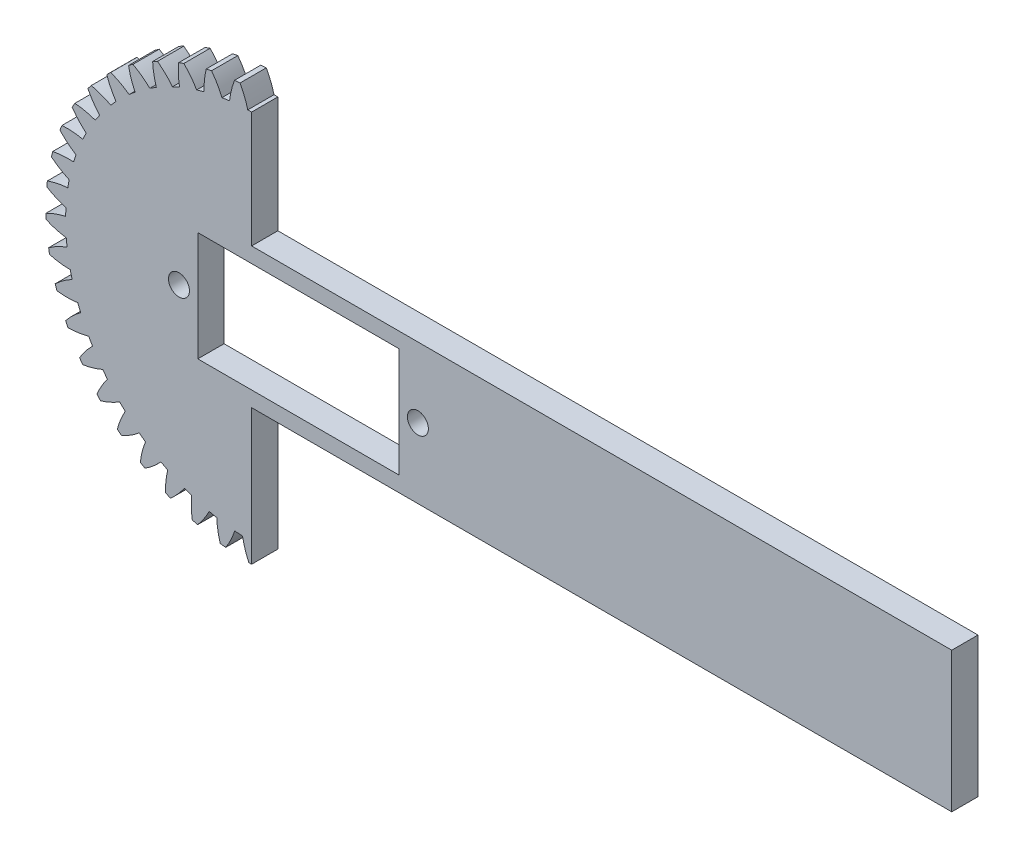
SolidWorks part; units mm, degrees
ref_plane "Front Plane" through (0, 0, 0) normal (0, 0, 1) x (1, 0, 0)
ref_plane "Top Plane" through (0, 0, 0) normal (0, 1, 0) x (1, 0, 0)
ref_plane "Right Plane" through (0, 0, 0) normal (1, 0, 0) x (0, 0, -1)
sketch "Model" plane through (0, 0, 0) normal (0, 0, 1) x (1, 0, 0)
  circle A0 centre (55.7791, 90.651) radius 15.95 construction
  arc A1 (32.4426, 93.4186) -> (32.3772, 92.7957) centre (55.7791, 90.651) ccw
  arc A2 (34.7806, 93.9041) -> (32.4426, 93.4186) centre (35.4255, 84.9273) ccw
  arc A3 (34.9343, 94.7759) -> (34.7806, 93.9041) centre (55.7791, 90.651) ccw
  arc A4 (32.9034, 96.0318) -> (34.9343, 94.7759) centre (38.6106, 102.9908) ccw
  arc A5 (33.0549, 96.6395) -> (32.9034, 96.0318) centre (55.7791, 90.651) ccw
  arc A6 (35.4377, 96.7949) -> (33.0549, 96.6395) centre (34.827, 87.8157) ccw
  arc A7 (35.7112, 97.6368) -> (35.4377, 96.7949) centre (55.7791, 90.651) ccw
  arc A8 (33.8749, 99.1631) -> (35.7112, 97.6368) centre (40.495, 105.2601) ccw
  arc A9 (34.1095, 99.7438) -> (33.8749, 99.1631) centre (55.7791, 90.651) ccw
  arc A10 (36.4907, 99.5661) -> (34.1095, 99.7438) centre (34.6363, 90.7592) ccw
  arc A11 (36.8788, 100.3617) -> (36.4907, 99.5661) centre (55.7791, 90.651) ccw
  arc A12 (35.2727, 102.1287) -> (36.8788, 100.3617) centre (42.677, 107.2451) ccw
  arc A13 (35.5859, 102.6711) -> (35.2727, 102.1287) centre (55.7791, 90.651) ccw
  arc A14 (37.9192, 102.1637) -> (35.5859, 102.6711) centre (34.8571, 93.7007) ccw
  arc A15 (38.4142, 102.8976) -> (37.9192, 102.1637) centre (55.7791, 90.651) ccw
  arc A16 (37.0697, 104.871) -> (38.4142, 102.8976) centre (45.1139, 108.907) ccw
  arc A17 (37.4553, 105.3645) -> (37.0697, 104.871) centre (55.7791, 90.651) ccw
  arc A18 (39.6953, 104.5373) -> (37.4553, 105.3645) centre (35.4852, 96.5828) ccw
  arc A19 (40.2876, 105.1951) -> (39.6953, 104.5373) centre (55.7791, 90.651) ccw
  arc A20 (39.2308, 107.3364) -> (40.2876, 105.1951) centre (47.7585, 110.2137) ccw
  arc A21 (39.6813, 107.7715) -> (39.2308, 107.3364) centre (55.7791, 90.651) ccw
  arc A22 (41.7844, 106.6406) -> (39.6813, 107.7715) centre (36.5082, 99.3494) ccw
  arc A23 (42.4625, 107.2096) -> (41.7844, 106.6406) centre (55.7791, 90.651) ccw
  arc A24 (41.714, 109.4771) -> (42.4625, 107.2096) centre (50.5591, 111.1395) ccw
  arc A25 (42.2207, 109.8452) -> (41.714, 109.4771) centre (55.7791, 90.651) ccw
  arc A26 (44.1459, 108.4327) -> (42.2207, 109.8452) centre (37.9063, 101.9467) ccw
  arc A27 (44.8966, 108.9018) -> (44.1459, 108.4327) centre (55.7791, 90.651) ccw
  arc A28 (44.471, 111.2514) -> (44.8966, 108.9018) centre (53.4614, 111.6666) ccw
  arc A29 (45.024, 111.5454) -> (44.471, 111.2514) centre (55.7791, 90.651) ccw
  arc A30 (46.7339, 109.8787) -> (45.024, 111.5454) centre (39.6523, 104.3242) ccw
  arc A31 (47.5425, 110.2387) -> (46.7339, 109.8787) centre (55.7791, 90.651) ccw
  arc A32 (47.4481, 112.6247) -> (47.5425, 110.2387) centre (56.4088, 111.7847) ccw
  arc A33 (48.0366, 112.8389) -> (47.4481, 112.6247) centre (55.7791, 90.651) ccw
  arc A34 (49.4979, 110.9504) -> (48.0366, 112.8389) centre (41.7122, 106.4356) ccw
  arc A35 (50.3488, 111.1944) -> (49.4979, 110.9504) centre (55.7791, 90.651) ccw
  arc A36 (50.5873, 113.5703) -> (50.3488, 111.1944) centre (59.3439, 111.4914) ccw
  arc A37 (51.1999, 113.7005) -> (50.5873, 113.5703) centre (55.7791, 90.651) ccw
  arc A38 (52.3842, 111.627) -> (51.1999, 113.7005) centre (44.0459, 108.2397) ccw
  arc A39 (53.2607, 111.7502) -> (52.3842, 111.627) centre (55.7791, 90.651) ccw
  arc A40 (53.8276, 114.0698) -> (53.2607, 111.7502) centre (62.2096, 110.7924) ccw
  arc A41 (54.4524, 114.1135) -> (53.8276, 114.0698) centre (55.7791, 90.651) ccw
  arc A42 (55.3365, 111.8954) -> (54.4524, 114.1135) centre (46.608, 109.7014) ccw
  arc A43 (56.2217, 111.8954) -> (55.3365, 111.8954) centre (55.7791, 90.651) ccw
  arc A44 (57.1058, 114.1135) -> (56.2217, 111.8954) centre (64.9502, 109.7014) ccw
  arc A45 (57.7306, 114.0698) -> (57.1058, 114.1135) centre (55.7791, 90.651) ccw
  arc A46 (58.2975, 111.7502) -> (57.7306, 114.0698) centre (49.3486, 110.7924) ccw
  arc A47 (59.174, 111.627) -> (58.2975, 111.7502) centre (55.7791, 90.651) ccw
  arc A48 (60.3583, 113.7005) -> (59.174, 111.627) centre (67.5123, 108.2397) ccw
  arc A49 (60.9709, 113.5703) -> (60.3583, 113.7005) centre (55.7791, 90.651) ccw
  arc A50 (61.2094, 111.1944) -> (60.9709, 113.5703) centre (52.2143, 111.4914) ccw
  arc A51 (62.0603, 110.9504) -> (61.2094, 111.1944) centre (55.7791, 90.651) ccw
  arc A52 (63.5216, 112.8389) -> (62.0603, 110.9504) centre (69.8459, 106.4356) ccw
  arc A53 (64.1101, 112.6247) -> (63.5216, 112.8389) centre (55.7791, 90.651) ccw
  arc A54 (64.0156, 110.2387) -> (64.1101, 112.6247) centre (55.1494, 111.7847) ccw
  arc A55 (64.8243, 109.8787) -> (64.0156, 110.2387) centre (55.7791, 90.651) ccw
  arc A56 (66.5342, 111.5454) -> (64.8243, 109.8787) centre (71.9058, 104.3242) ccw
  arc A57 (67.0872, 111.2514) -> (66.5342, 111.5454) centre (55.7791, 90.651) ccw
  arc A58 (66.6616, 108.9018) -> (67.0872, 111.2514) centre (58.0968, 111.6666) ccw
  arc A59 (67.4122, 108.4327) -> (66.6616, 108.9018) centre (55.7791, 90.651) ccw
  arc A60 (69.3375, 109.8452) -> (67.4122, 108.4327) centre (73.6518, 101.9467) ccw
  arc A61 (69.8442, 109.4771) -> (69.3375, 109.8452) centre (55.7791, 90.651) ccw
  arc A62 (69.0957, 107.2096) -> (69.8442, 109.4771) centre (60.999, 111.1395) ccw
  arc A63 (69.7738, 106.6406) -> (69.0957, 107.2096) centre (55.7791, 90.651) ccw
  arc A64 (71.8768, 107.7715) -> (69.7738, 106.6406) centre (75.05, 99.3494) ccw
  arc A65 (72.3274, 107.3364) -> (71.8768, 107.7715) centre (55.7791, 90.651) ccw
  arc A66 (71.2706, 105.1951) -> (72.3274, 107.3364) centre (63.7997, 110.2137) ccw
  arc A67 (71.8629, 104.5373) -> (71.2706, 105.1951) centre (55.7791, 90.651) ccw
  arc A68 (74.1029, 105.3645) -> (71.8629, 104.5373) centre (76.073, 96.5828) ccw
  arc A69 (74.4885, 104.871) -> (74.1029, 105.3645) centre (55.7791, 90.651) ccw
  arc A70 (73.144, 102.8976) -> (74.4885, 104.871) centre (66.4442, 108.907) ccw
  arc A71 (73.639, 102.1637) -> (73.144, 102.8976) centre (55.7791, 90.651) ccw
  arc A72 (75.9723, 102.6711) -> (73.639, 102.1637) centre (76.7011, 93.7007) ccw
  arc A73 (76.2855, 102.1287) -> (75.9723, 102.6711) centre (55.7791, 90.651) ccw
  arc A74 (74.6794, 100.3617) -> (76.2855, 102.1287) centre (68.8812, 107.2451) ccw
  arc A75 (75.0674, 99.5661) -> (74.6794, 100.3617) centre (55.7791, 90.651) ccw
  arc A76 (77.4487, 99.7438) -> (75.0674, 99.5661) centre (76.9219, 90.7592) ccw
  arc A77 (77.6833, 99.1631) -> (77.4487, 99.7438) centre (55.7791, 90.651) ccw
  arc A78 (75.8469, 97.6368) -> (77.6833, 99.1631) centre (71.0632, 105.2601) ccw
  arc A79 (76.1205, 96.7949) -> (75.8469, 97.6368) centre (55.7791, 90.651) ccw
  arc A80 (78.5033, 96.6395) -> (76.1205, 96.7949) centre (76.7312, 87.8157) ccw
  arc A81 (78.6548, 96.0318) -> (78.5033, 96.6395) centre (55.7791, 90.651) ccw
  arc A82 (76.6239, 94.7759) -> (78.6548, 96.0318) centre (72.9476, 102.9908) ccw
  arc A83 (76.7776, 93.9041) -> (76.6239, 94.7759) centre (55.7791, 90.651) ccw
  arc A84 (79.1155, 93.4186) -> (76.7776, 93.9041) centre (76.1327, 84.9273) ccw
  arc A85 (79.181, 92.7957) -> (79.1155, 93.4186) centre (55.7791, 90.651) ccw
  arc A86 (76.9951, 91.8347) -> (79.181, 92.7957) centre (74.4979, 100.4813) ccw
  arc A87 (77.026, 90.9501) -> (76.9951, 91.8347) centre (55.7791, 90.651) ccw
  arc A88 (79.2736, 90.1439) -> (77.026, 90.9501) centre (75.138, 82.1503) ccw
  arc A89 (79.2518, 89.5179) -> (79.2736, 90.1439) centre (55.7791, 90.651) ccw
  arc A90 (76.9534, 88.8705) -> (79.2518, 89.5179) centre (75.6839, 97.7805) ccw
  arc A91 (76.8608, 87.9902) -> (76.9534, 88.8705) centre (55.7791, 90.651) ccw
  arc A92 (78.9744, 86.879) -> (76.8608, 87.9902) centre (73.7666, 79.5388) ccw
  arc A93 (78.8656, 86.2622) -> (78.9744, 86.879) centre (55.7791, 90.651) ccw
  arc A94 (76.4995, 85.9409) -> (78.8656, 86.2622) centre (76.4824, 94.9409) ccw
  arc A95 (76.2854, 85.082) -> (76.4995, 85.9409) centre (55.7791, 90.651) ccw
  arc A96 (78.2237, 83.6875) -> (76.2854, 85.082) centre (72.045, 77.1436) ccw
  arc A97 (78.0302, 83.0919) -> (78.2237, 83.6875) centre (55.7791, 90.651) ccw
  arc A98 (75.6423, 83.103) -> (78.0302, 83.0919) centre (76.8779, 92.0178) ccw
  arc A99 (75.3107, 82.2823) -> (75.6423, 83.103) centre (55.7791, 90.651) ccw
  arc A100 (77.0362, 80.6316) -> (75.3107, 82.2823) centre (70.0068, 75.0112) ccw
  arc A101 (76.7616, 80.0687) -> (77.0362, 80.6316) centre (55.7791, 90.651) ccw
  arc A102 (74.3986, 80.4121) -> (76.7616, 80.0687) centre (76.8628, 89.0681) ccw
  arc A103 (73.956, 79.6455) -> (74.3986, 80.4121) centre (55.7791, 90.651) ccw
  arc A104 (75.4349, 77.7707) -> (73.956, 79.6455) centre (67.6917, 73.1833) ccw
  arc A105 (75.0846, 77.2515) -> (75.4349, 77.7707) centre (55.7791, 90.651) ccw
  arc A106 (72.7924, 77.9204) -> (75.0846, 77.2515) centre (76.4374, 86.1492) ccw
  arc A107 (72.2474, 77.2228) -> (72.7924, 77.9204) centre (55.7791, 90.651) ccw
  arc A108 (73.451, 75.1605) -> (72.2474, 77.2228) centre (65.1448, 71.6954) ccw
  arc A109 (73.0319, 74.6951) -> (73.451, 75.1605) centre (55.7791, 90.651) ccw
  arc A110 (70.8551, 75.6765) -> (73.0319, 74.6951) centre (75.6098, 83.318) ccw
  arc A111 (70.2183, 75.0616) -> (70.8551, 75.6765) centre (55.7791, 90.651) ccw
  arc A112 (71.1231, 72.8518) -> (70.2183, 75.0616) centre (62.4155, 70.5764) ccw
  arc A113 (70.6434, 72.4492) -> (71.1231, 72.8518) centre (55.7791, 90.651) ccw
  arc A114 (68.6243, 73.724) -> (70.6434, 72.4492) centre (74.3963, 80.6294) ccw
  arc A115 (67.9082, 73.2037) -> (68.6243, 73.724) centre (55.7791, 90.651) ccw
  arc A116 (68.4967, 70.8895) -> (67.9082, 73.2037) centre (59.5571, 69.8482) ccw
  arc A117 (67.9655, 70.5577) -> (68.4967, 70.8895) centre (55.7791, 90.651) ccw
  arc A118 (66.1435, 72.1011) -> (67.9655, 70.5577) centre (72.8203, 78.136) ccw
  arc A119 (65.3619, 71.6855) -> (66.1435, 72.1011) centre (55.7791, 90.651) ccw
  arc A120 (65.6226, 69.3119) -> (65.3619, 71.6855) centre (56.6252, 69.5248) ccw
  arc A121 (65.0505, 69.0572) -> (65.6226, 69.3119) centre (55.7791, 90.651) ccw
  arc A122 (63.461, 70.8391) -> (65.0505, 69.0572) centre (70.9128, 75.8861) ccw
  arc A123 (62.6292, 70.5364) -> (63.461, 70.8391) centre (55.7791, 90.651) ccw
  arc A124 (62.557, 68.1496) -> (62.6292, 70.5364) centre (53.6767, 69.6127) ccw
  arc A125 (61.955, 67.977) -> (62.557, 68.1496) centre (55.7791, 90.651) ccw
  arc A126 (60.629, 69.9628) -> (61.955, 67.977) centre (68.7106, 73.9236) ccw
  arc A127 (59.7631, 69.7788) -> (60.629, 69.9628) centre (55.7791, 90.651) ccw
  arc A128 (59.3595, 67.4253) -> (59.7631, 69.7788) centre (50.7692, 70.11) ccw
  arc A129 (58.7393, 67.3381) -> (59.3595, 67.4253) centre (55.7791, 90.651) ccw
  arc A130 (57.7025, 69.4892) -> (58.7393, 67.3381) centre (66.2567, 72.2866) ccw
  arc A131 (56.8195, 69.4274) -> (57.7025, 69.4892) centre (55.7791, 90.651) ccw
  arc A132 (56.0922, 67.1531) -> (56.8195, 69.4274) centre (47.9592, 71.0071) ccw
  arc A133 (55.4659, 67.1531) -> (56.0922, 67.1531) centre (55.7791, 90.651) ccw
  arc A134 (54.7387, 69.4274) -> (55.4659, 67.1531) centre (63.599, 71.0071) ccw
  arc A135 (53.8556, 69.4892) -> (54.7387, 69.4274) centre (55.7791, 90.651) ccw
  arc A136 (52.8189, 67.3381) -> (53.8556, 69.4892) centre (45.3014, 72.2866) ccw
  arc A137 (52.1987, 67.4253) -> (52.8189, 67.3381) centre (55.7791, 90.651) ccw
  arc A138 (51.7951, 69.7788) -> (52.1987, 67.4253) centre (60.789, 70.11) ccw
  arc A139 (50.9292, 69.9628) -> (51.7951, 69.7788) centre (55.7791, 90.651) ccw
  arc A140 (49.6032, 67.977) -> (50.9292, 69.9628) centre (42.8476, 73.9236) ccw
  arc A141 (49.0012, 68.1496) -> (49.6032, 67.977) centre (55.7791, 90.651) ccw
  arc A142 (48.929, 70.5364) -> (49.0012, 68.1496) centre (57.8815, 69.6127) ccw
  arc A143 (48.0972, 70.8391) -> (48.929, 70.5364) centre (55.7791, 90.651) ccw
  arc A144 (46.5077, 69.0572) -> (48.0972, 70.8391) centre (40.6454, 75.8861) ccw
  arc A145 (45.9355, 69.3119) -> (46.5077, 69.0572) centre (55.7791, 90.651) ccw
  arc A146 (46.1962, 71.6855) -> (45.9355, 69.3119) centre (54.933, 69.5248) ccw
  arc A147 (45.4147, 72.1011) -> (46.1962, 71.6855) centre (55.7791, 90.651) ccw
  arc A148 (43.5927, 70.5577) -> (45.4147, 72.1011) centre (38.7378, 78.136) ccw
  arc A149 (43.0615, 70.8895) -> (43.5927, 70.5577) centre (55.7791, 90.651) ccw
  arc A150 (43.65, 73.2037) -> (43.0615, 70.8895) centre (52.0011, 69.8482) ccw
  arc A151 (42.9339, 73.724) -> (43.65, 73.2037) centre (55.7791, 90.651) ccw
  arc A152 (40.9148, 72.4492) -> (42.9339, 73.724) centre (37.1619, 80.6294) ccw
  arc A153 (40.435, 72.8518) -> (40.9148, 72.4492) centre (55.7791, 90.651) ccw
  arc A154 (41.3399, 75.0616) -> (40.435, 72.8518) centre (49.1426, 70.5764) ccw
  arc A155 (40.7031, 75.6765) -> (41.3399, 75.0616) centre (55.7791, 90.651) ccw
  arc A156 (38.5263, 74.6951) -> (40.7031, 75.6765) centre (35.9484, 83.318) ccw
  arc A157 (38.1072, 75.1605) -> (38.5263, 74.6951) centre (55.7791, 90.651) ccw
  arc A158 (39.3108, 77.2228) -> (38.1072, 75.1605) centre (46.4134, 71.6954) ccw
  arc A159 (38.7658, 77.9204) -> (39.3108, 77.2228) centre (55.7791, 90.651) ccw
  arc A160 (36.4736, 77.2515) -> (38.7658, 77.9204) centre (35.1208, 86.1492) ccw
  arc A161 (36.1233, 77.7707) -> (36.4736, 77.2515) centre (55.7791, 90.651) ccw
  arc A162 (37.6022, 79.6455) -> (36.1233, 77.7707) centre (43.8664, 73.1833) ccw
  arc A163 (37.1596, 80.4121) -> (37.6022, 79.6455) centre (55.7791, 90.651) ccw
  arc A164 (34.7966, 80.0687) -> (37.1596, 80.4121) centre (34.6953, 89.0681) ccw
  arc A165 (34.522, 80.6316) -> (34.7966, 80.0687) centre (55.7791, 90.651) ccw
  arc A166 (36.2474, 82.2823) -> (34.522, 80.6316) centre (41.5513, 75.0112) ccw
  arc A167 (35.9158, 83.103) -> (36.2474, 82.2823) centre (55.7791, 90.651) ccw
  arc A168 (33.528, 83.0919) -> (35.9158, 83.103) centre (34.6802, 92.0178) ccw
  arc A169 (33.3345, 83.6875) -> (33.528, 83.0919) centre (55.7791, 90.651) ccw
  arc A170 (35.2728, 85.082) -> (33.3345, 83.6875) centre (39.5132, 77.1436) ccw
  arc A171 (35.0587, 85.9409) -> (35.2728, 85.082) centre (55.7791, 90.651) ccw
  arc A172 (32.6925, 86.2622) -> (35.0587, 85.9409) centre (35.0758, 94.9409) ccw
  arc A173 (32.5838, 86.879) -> (32.6925, 86.2622) centre (55.7791, 90.651) ccw
  arc A174 (34.6973, 87.9902) -> (32.5838, 86.879) centre (37.7916, 79.5388) ccw
  arc A175 (34.6048, 88.8705) -> (34.6973, 87.9902) centre (55.7791, 90.651) ccw
  arc A176 (32.3064, 89.5179) -> (34.6048, 88.8705) centre (35.8743, 97.7805) ccw
  arc A177 (32.2846, 90.1439) -> (32.3064, 89.5179) centre (55.7791, 90.651) ccw
  arc A178 (34.5322, 90.9501) -> (32.2846, 90.1439) centre (36.4201, 82.1503) ccw
  arc A179 (34.5631, 91.8347) -> (34.5322, 90.9501) centre (55.7791, 90.651) ccw
  arc A180 (32.3772, 92.7957) -> (34.5631, 91.8347) centre (37.0603, 100.4813) ccw
  circle A181 centre (55.7791, 90.651) radius 2.5
extrude "Boss-Extrude1" add sketch "Model" along normal blind 3
sketch "Sketch2" plane through (0, 0, 3) normal (0, 0, 1) x (1, 0, 0)
  line L0 (55.7791, 90.651) -> (55.7791, 117.1598)
  line L1 (55.7791, 117.1598) -> (88.793, 117.1598)
  line L2 (88.793, 117.1598) -> (88.793, 58.0456)
  line L3 (88.793, 58.0456) -> (55.7791, 58.0456)
  line L4 (55.7791, 58.0456) -> (55.7791, 90.651)
extrude "Cut-Extrude1" cut sketch "Sketch2" against normal blind 3
sketch "Sketch5" plane through (0, 0, 0) normal (0, 0, 1) x (1, 0, 0)
  line L0 (53.2791, 90.651) -> (91.9422, 90.651) construction
  line L1 (135.7791, 98.651) -> (53.2791, 98.651)
  line L2 (135.7791, 98.651) -> (135.7791, 82.651)
  line L3 (53.2791, 98.651) -> (53.2791, 82.651)
  line L4 (135.7791, 82.651) -> (53.2791, 82.651)
  line L5 (53.2791, 90.651) -> (135.7791, 90.651) construction
  line L6 (94.5291, 98.651) -> (94.5291, 82.651) construction
  line L7 (55.7791, 111.9) -> (55.7791, 93.151) construction
  arc A1 (55.7791, 93.151) -> (55.7791, 88.151) centre (55.7791, 90.651) ccw construction
  point P6 (94.5291, 90.651)
  dimension "D1" = 16
  dimension "D2" = 80
extrude "Boss-Extrude2" add sketch "Sketch5" along normal blind 3
sketch "Sketch6" plane through (0, 0, 3) normal (0, 0, 1) x (1, 0, 0)
  line L0 (55.7791, 98.651) -> (55.7791, 82.651) construction
  line L1 (55.7791, 90.651) -> (99.5621, 90.651) construction
  line L3 (49.6291, 84.401) -> (72.6291, 84.401)
  line L4 (49.6291, 84.401) -> (49.6291, 96.901)
  line L5 (49.6291, 96.901) -> (72.6291, 96.901)
  line L6 (72.6291, 84.401) -> (72.6291, 96.901)
  line L7 (61.1291, 96.901) -> (61.1291, 84.401) construction
  line L8 (49.6291, 90.651) -> (72.6291, 90.651) construction
  circle A0 centre (47.4791, 90.651) radius 1.2
  circle A1 centre (74.7791, 90.651) radius 1.2
  circle A2 centre (55.7791, 90.651) radius 2.5214 construction
  point P6 (61.1291, 90.651)
  dimension "D1" = 2.4
  dimension "D5" = 27.3
  dimension "D6" = 6.15
  dimension "D2" = 12.5
  dimension "D3" = 23
  dimension "D4" = 2.15
extrude "Cut-Extrude3" cut sketch "Sketch6" against normal blind 3
sketch "Sketch7" plane through (0, 0, 0) normal (0, 0, 1) x (1, 0, 0)
  circle A0 centre (55.7791, 90.651) radius 21.249 construction
  circle A1 centre (55.7791, 90.651) radius 22.5 construction
  dimension "D1" = 45
